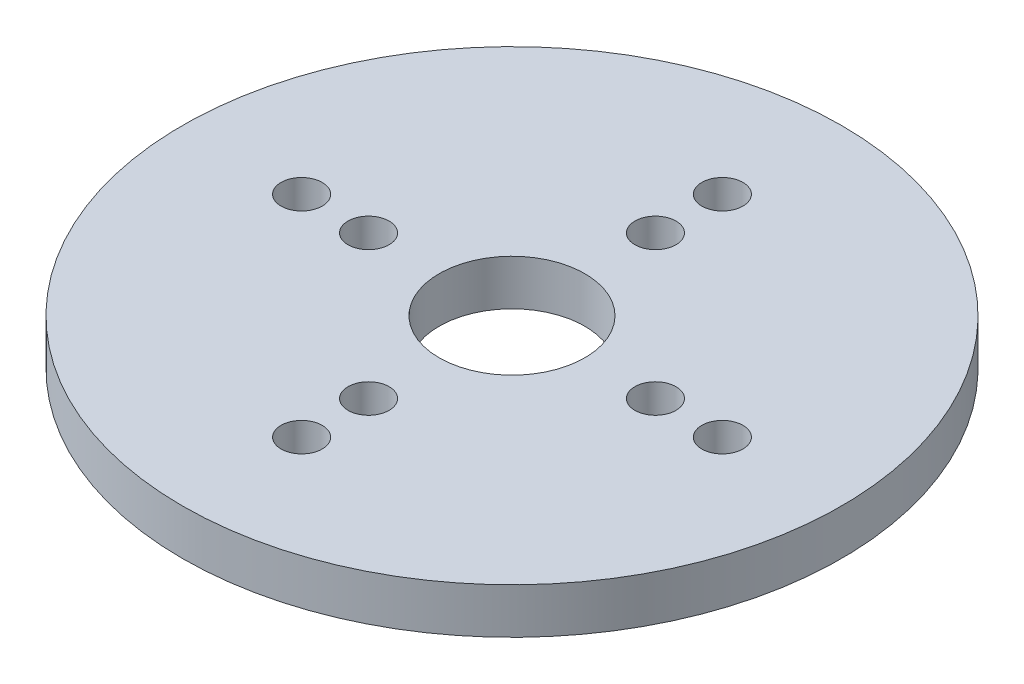
SolidWorks part; units mm, degrees
ref_plane "Front Plane" through (0, 0, 0) normal (0, 0, 1) x (1, 0, 0)
ref_plane "Top Plane" through (0, 0, 0) normal (0, 1, 0) x (1, 0, 0)
ref_plane "Right Plane" through (0, 0, 0) normal (1, 0, 0) x (0, 0, -1)
sketch "Sketch1" plane through (0, 0, 0) normal (0, 1, 0) x (1, 0, 0)
  line L0 (0, -48.2646) -> (0, -8.2647) construction
  line L1 (0, -8.2647) -> (0, 48.2646) construction
  line L2 (0, 0) -> (-42.3088, 0) construction
  line L3 (0, 0) -> (42.3088, 0) construction
  line L4 (0, -8.2647) -> (15, -8.2647) construction
  line L6 (15, -8.2647) -> (22, -8.2647) construction
  line L7 (0, -8.2647) -> (0, -23.2647) construction
  line L8 (0, -23.2647) -> (0, -30.2647) construction
  line L9 (0, -8.2647) -> (-15, -8.2647) construction
  line L10 (-15, -8.2647) -> (-22, -8.2647) construction
  line L11 (0, -8.2647) -> (0, 6.7353) construction
  line L12 (0, 6.7353) -> (0, 13.7353) construction
  line L17 (0, -8.2647) -> (0, -40.6446)
  circle A22 centre (15, -8.2647) radius 2.15
  circle A23 centre (22, -8.2647) radius 2.15
  circle A24 centre (0, -23.2647) radius 2.15
  circle A25 centre (0, -30.2647) radius 2.15
  circle A26 centre (-15, -8.2647) radius 2.15
  circle A27 centre (-22, -8.2647) radius 2.15
  circle A28 centre (0, 6.7353) radius 2.15
  circle A29 centre (0, 13.7353) radius 2.15
  circle A30 centre (0, -8.2647) radius 7.62
  circle A31 centre (0, -8.2647) radius 34.4649
  point P3 (0, 0)
  point P27 (0, -8.2647)
  dimension "D6" = 15
  dimension "D7" = 7
  dimension "D10" = 4
  dimension "D11" = 15.24
  dimension "D8" = 4.3
  dimension "D9" = 4.3
  dimension "D2" = 68.9297
  dimension "D5" = 39.9999
extrude "Boss-Extrude1" add sketch "Sketch1" along normal blind 4.7625
